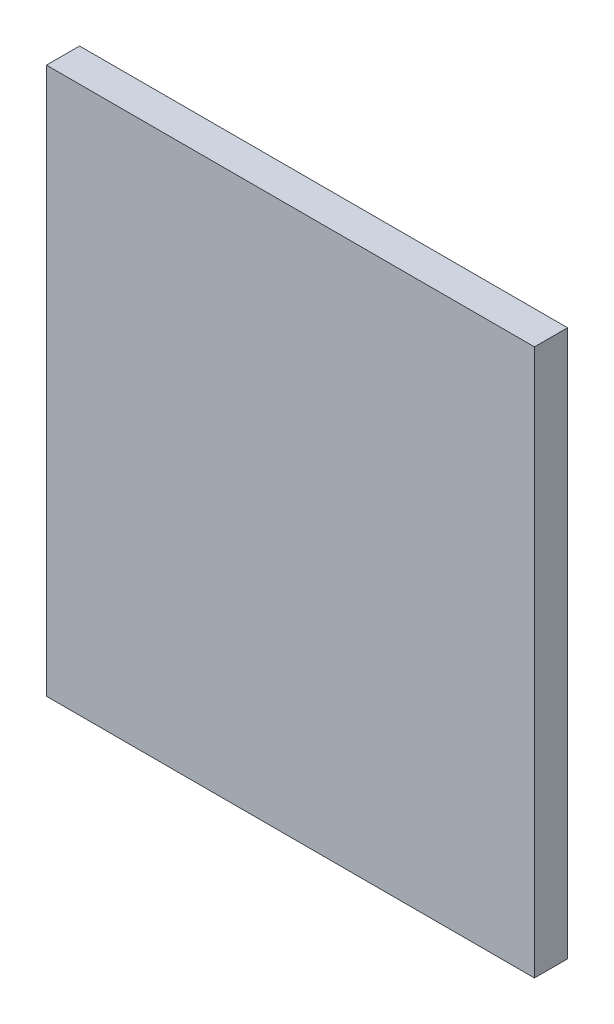
SolidWorks part; units mm, degrees
material "Acrylic (Medium-high impact)"
ref_plane "Front Plane" through (0, 0, 0) normal (0, 0, 1) x (1, 0, 0)
ref_plane "Top Plane" through (0, 0, 0) normal (0, 1, 0) x (1, 0, 0)
ref_plane "Right Plane" through (0, 0, 0) normal (1, 0, 0) x (0, 0, -1)
sketch "Sketch1" plane through (0, 0, 0) normal (0, 0, 1) x (1, 0, 0)
  line L1 (1.3555, 12.7291) -> (30.8355, 12.7291)
  line L2 (1.3555, 12.7291) -> (1.3555, -20.2909)
  line L3 (1.3555, -20.2909) -> (30.8355, -20.2909)
  line L4 (30.8355, 12.7291) -> (30.8355, -20.2909)
  dimension "D1" = 33.02
  dimension "D2" = 29.48
extrude "Boss-Extrude1" add sketch "Sketch1" along normal blind 2
